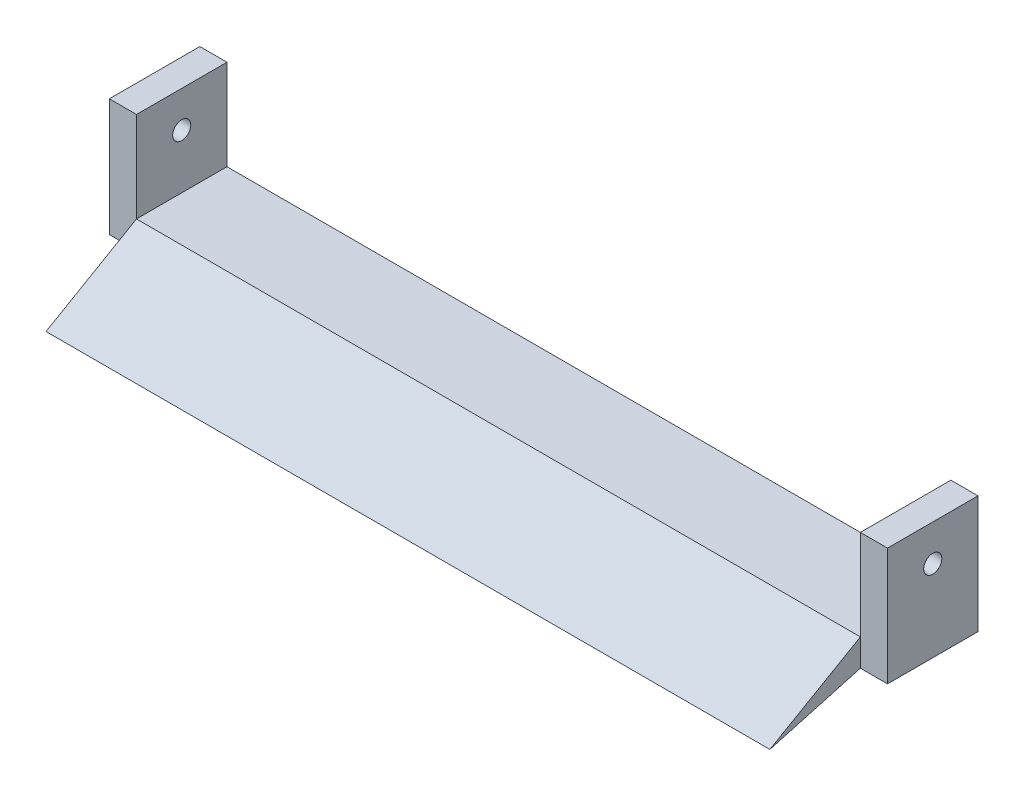
SolidWorks part; units mm, degrees
ref_plane "Front Plane" through (0, 0, 0) normal (0, 0, 1) x (1, 0, 0)
ref_plane "Top Plane" through (0, 0, 0) normal (0, 1, 0) x (1, 0, 0)
ref_plane "Right Plane" through (0, 0, 0) normal (1, 0, 0) x (0, 0, -1)
sketch "Sketch1" plane through (0, 0, 0) normal (0, 0, 1) x (1, 0, 0)
  line L0 (200, 32.5) -> (215, 32.5)
  line L1 (-215, -32.5) -> (215, -32.5)
  line L2 (-215, -32.5) -> (-215, 32.5)
  line L3 (-215, 32.5) -> (-200, 32.5)
  line L4 (215, -32.5) -> (215, 32.5)
  line L5 (-215, -32.5) -> (215, 32.5) construction
  line L6 (-215, 32.5) -> (215, -32.5) construction
  line L8 (-200, 32.5) -> (-200, -17.5)
  line L9 (-200, -17.5) -> (200, -17.5)
  line L10 (200, 32.5) -> (200, -17.5)
  point P0 (0, 0)
  point P12 (0, 0)
  dimension "D1" = 400
  dimension "D2" = 430
  dimension "D3" = 15
  dimension "D4" = 50
  dimension "D5" = 65
extrude "Boss-Extrude1" add sketch "Sketch1" along normal blind 50
sketch "Sketch2" plane through (215, 0, 0) normal (1, 0, 0) x (0, 0, -1)
  line L0 (-25, 32.5) -> (-25, -32.5) construction
  line L1 (-50, 32.5) -> (0, 32.5) construction
  line L2 (-50, -32.5) -> (0, -32.5) construction
  circle A0 centre (-25, 12.5) radius 5
  dimension "D1" = 10
  dimension "D2" = 20
extrude "Cut-Extrude1" cut sketch "Sketch2" against normal blind 477
sketch "Sketch3" plane through (0, 0, 0) normal (1, 0, 0) x (0, 0, -1)
  line L0 (-50, -32.5) -> (-100, -46.3675)
  line L1 (-100, -46.3675) -> (-50, -17.5)
  line L2 (-50, -32.5) -> (-50, 32.5) construction
  line L3 (-50, -17.5) -> (-50, -32.5)
  dimension "D1" = 15
  dimension "D2" = 120
  dimension "D3" = 50
extrude "Boss-Extrude2" add sketch "Sketch3" along normal mid plane 400
